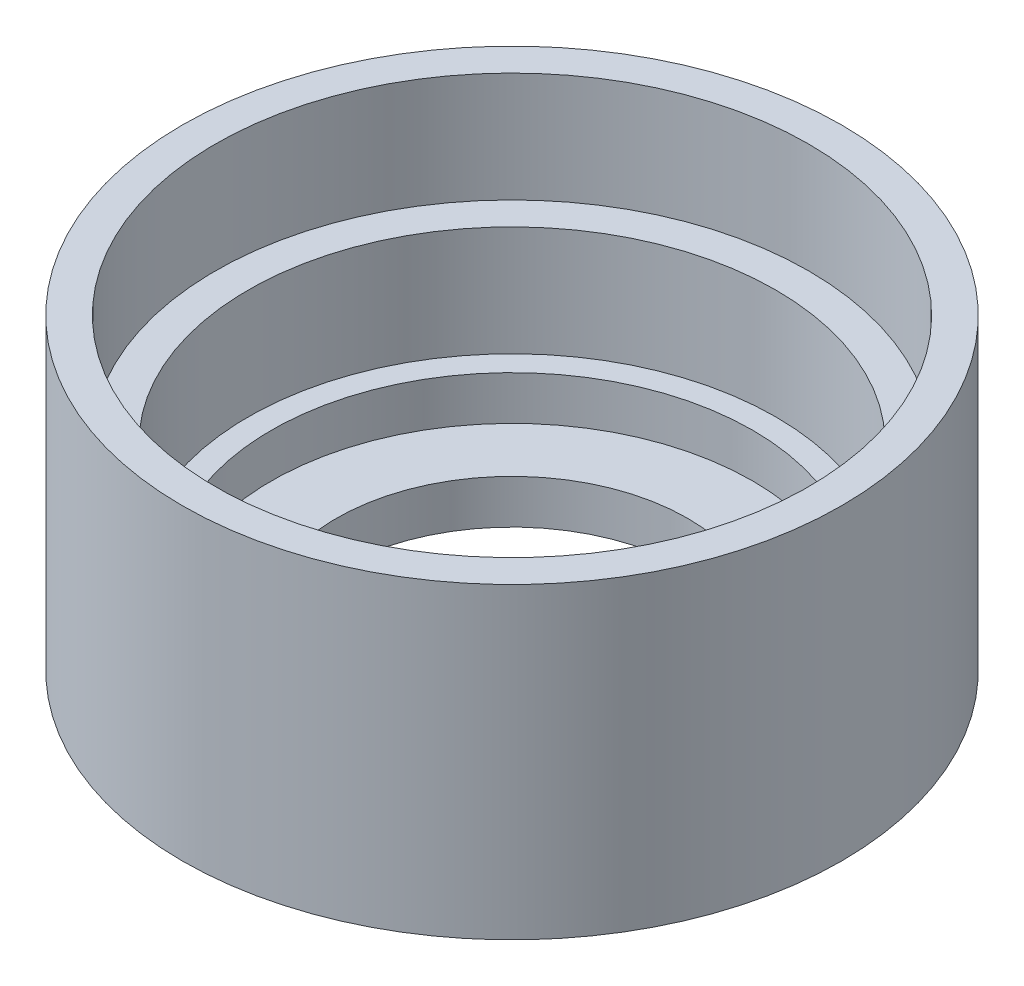
SolidWorks part; units mm, degrees
ref_plane "前视基准面" through (0, 0, 0) normal (0, 0, 1) x (1, 0, 0)
ref_plane "上视基准面" through (0, 0, 0) normal (0, 1, 0) x (1, 0, 0)
ref_plane "右视基准面" through (0, 0, 0) normal (1, 0, 0) x (0, 0, -1)
other "Configuration Table"
sketch "草图1" plane through (0, 0, 0) normal (0, 0, 1) x (1, 0, 0)
  line L0 (8, 0) -> (15, 0)
  line L1 (15, 0) -> (15, 14)
  line L2 (15, 14) -> (13.5, 14)
  line L3 (13.5, 14) -> (13.5, 9)
  line L4 (13.5, 9) -> (12, 9)
  line L5 (12, 9) -> (12, 4)
  line L6 (12, 4) -> (10.95, 4)
  line L7 (10.95, 4) -> (10.95, 2)
  line L8 (10.95, 2) -> (8, 2)
  line L9 (8, 2) -> (8, 0)
  line L10 (0, 0) -> (0, 18.5313) construction
  dimension "D1" = 8
  dimension "D2" = 0
  dimension "D3" = 15
  dimension "D4" = 2
  dimension "D5" = 4
  dimension "D6" = 10.95
  dimension "D7" = 12
  dimension "D8" = 13.5
  dimension "D9" = 5
  dimension "D10" = 14
revolve "旋转1" add sketch "草图1" angle 360 about L10
